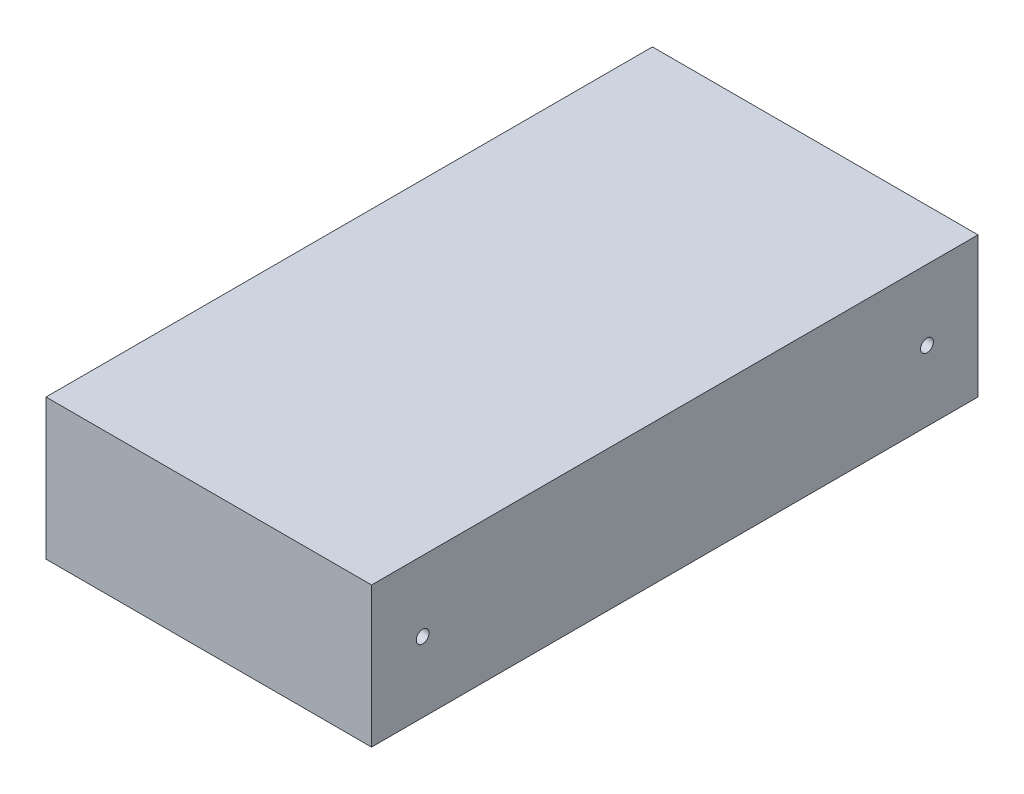
SolidWorks part; units mm, degrees
ref_plane "前视基准面" through (0, 0, 0) normal (0, 0, 1) x (1, 0, 0)
ref_plane "上视基准面" through (0, 0, 0) normal (0, 1, 0) x (1, 0, 0)
ref_plane "右视基准面" through (0, 0, 0) normal (1, 0, 0) x (0, 0, -1)
sketch "草图1" plane through (0, 0, 0) normal (0, 1, 0) x (1, 0, 0)
  line L0 (-25.5, -47.5) -> (-25.5, 47.5)
  line L1 (-25.5, -47.5) -> (25.5, -47.5)
  line L2 (-25.5, 47.5) -> (25.5, 47.5)
  line L3 (25.5, -47.5) -> (25.5, 47.5)
  line L4 (-25.5, -47.5) -> (25.5, 47.5) construction
  line L5 (-25.5, 47.5) -> (25.5, -47.5) construction
  point P1 (0, 0)
extrude "凸台-拉伸1" add sketch "草图1" along normal blind 22
sketch "草图2" plane through (25.5, 0, 0) normal (1, 0, 0) x (0, 0, -1)
  circle A0 centre (-39.5, 11) radius 1
extrude "切除-拉伸1" cut sketch "草图2" against normal up to next (51 mm away)
mirror "镜向1" about plane through (0, 0, 0) normal (0, 0, 1) of "切除-拉伸1"
